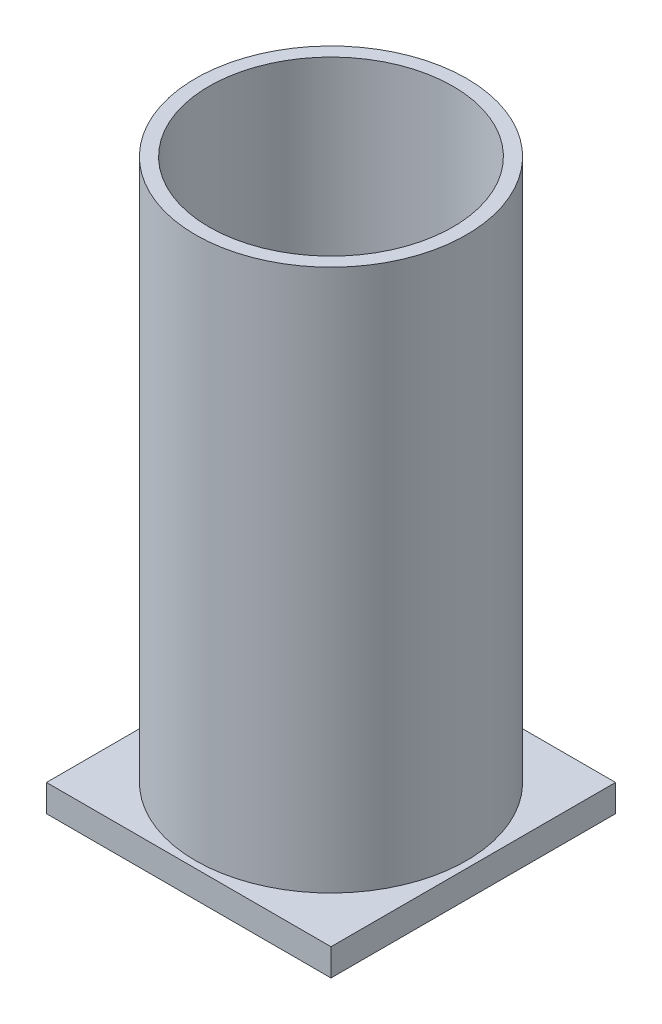
SolidWorks part; units mm, degrees
ref_plane "Front Plane" through (0, 0, 0) normal (0, 0, 1) x (1, 0, 0)
ref_plane "Top Plane" through (0, 0, 0) normal (0, 1, 0) x (1, 0, 0)
ref_plane "Right Plane" through (0, 0, 0) normal (1, 0, 0) x (0, 0, -1)
sketch "Sketch2" plane through (0, 0, 0) normal (0, 1, 0) x (1, 0, 0)
  circle A0 centre (0, 0) radius 50
  circle A3 centre (0, 0) radius 45
  dimension "D1" = 100
  dimension "D2" = 90
extrude "Boss-Extrude3" add sketch "Sketch2" along normal blind 200
sketch "Sketch4" plane through (0, 0, 0) normal (0, 1, 0) x (1, 0, 0)
  line L1 (-52.5, 52.5) -> (52.5, 52.5)
  line L2 (-52.5, 52.5) -> (-52.5, -52.5)
  line L3 (-52.5, -52.5) -> (52.5, -52.5)
  line L4 (52.5, 52.5) -> (52.5, -52.5)
  line L5 (-52.5, 52.5) -> (52.5, -52.5) construction
  line L6 (-52.5, -52.5) -> (52.5, 52.5) construction
  point P0 (0, 0)
  dimension "D1" = 105
  dimension "D2" = 105
extrude "Boss-Extrude5" add sketch "Sketch4" against normal blind 10
